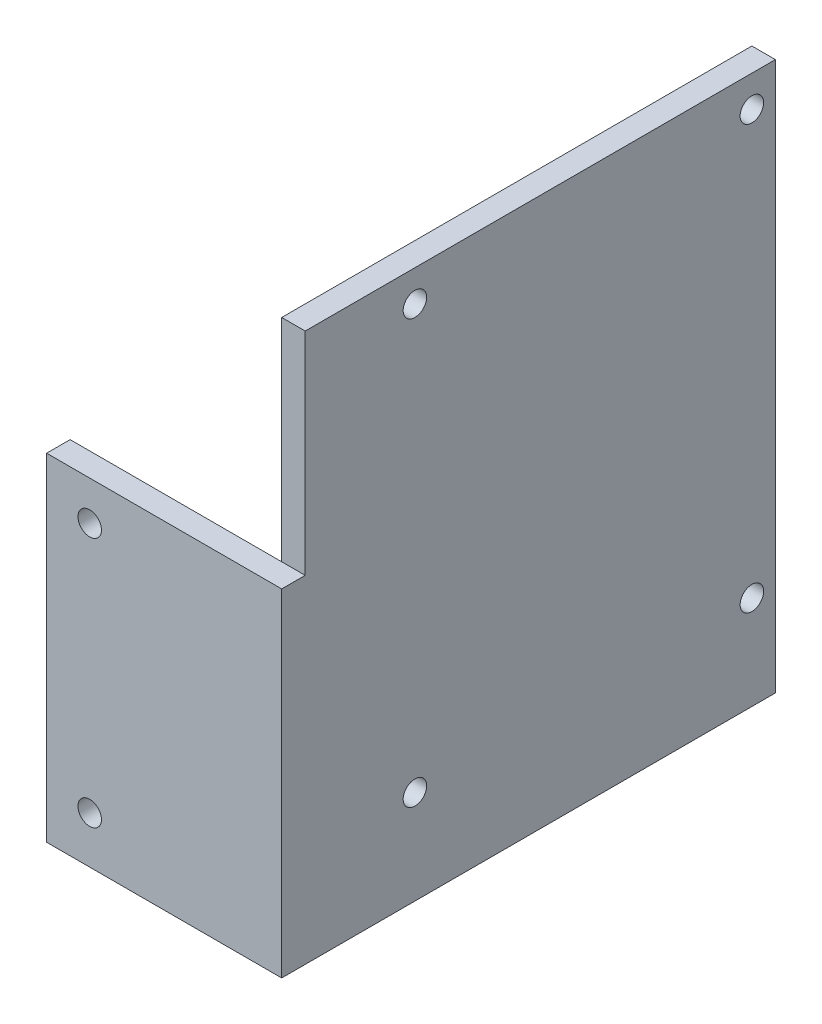
SolidWorks part; units mm, degrees
ref_plane "Alzado" through (0, 0, 0) normal (0, 0, 1) x (1, 0, 0)
ref_plane "Planta" through (0, 0, 0) normal (0, 1, 0) x (1, 0, 0)
ref_plane "Vista lateral" through (0, 0, 0) normal (1, 0, 0) x (0, 0, -1)
sketch "Croquis1" plane through (0, 0, 0) normal (0, 0, 1) x (1, 0, 0)
  line L1 (-40.3786, 16.4678) -> (-10.3786, 16.4678)
  line L2 (-40.3786, 16.4678) -> (-40.3786, -26.5322)
  line L3 (-40.3786, -26.5322) -> (-10.3786, -26.5322)
  line L4 (-10.3786, 16.4678) -> (-10.3786, -26.5322)
  circle A0 centre (-34.8786, 11.4678) radius 1.5
  circle A1 centre (-34.8786, -20.5322) radius 1.5
  dimension "D3" = 24.5
  dimension "D1" = 30
  dimension "D2" = 43
  dimension "D4" = 24.5
  dimension "D5" = 6
  dimension "D6" = 32
extrude "Saliente-Extruir1" add sketch "Croquis1" along normal blind 3
sketch "Croquis2" plane through (-10.3786, 0, 0) normal (1, 0, 0) x (0, 0, -1)
  line L5 (0, -26.5322) -> (60, -26.5322)
  line L6 (0, -26.5322) -> (0, 43.4678)
  line L7 (0, 43.4678) -> (60, 43.4678)
  line L8 (60, -26.5322) -> (60, 43.4678)
  circle A0 centre (57, 39.4678) radius 1.5
  circle A1 centre (14, 39.4678) radius 1.5
  circle A2 centre (14, -14.5322) radius 1.5
  circle A3 centre (57, -14.5322) radius 1.5
  dimension "D3" = 3
  dimension "D1" = 60
  dimension "D2" = 70
  dimension "D4" = 4
  dimension "D7" = 43
  dimension "D8" = 54
  dimension "D5" = 2
  dimension "D6" = 2
extrude "Saliente-Extruir2" add sketch "Croquis2" against normal blind 3
